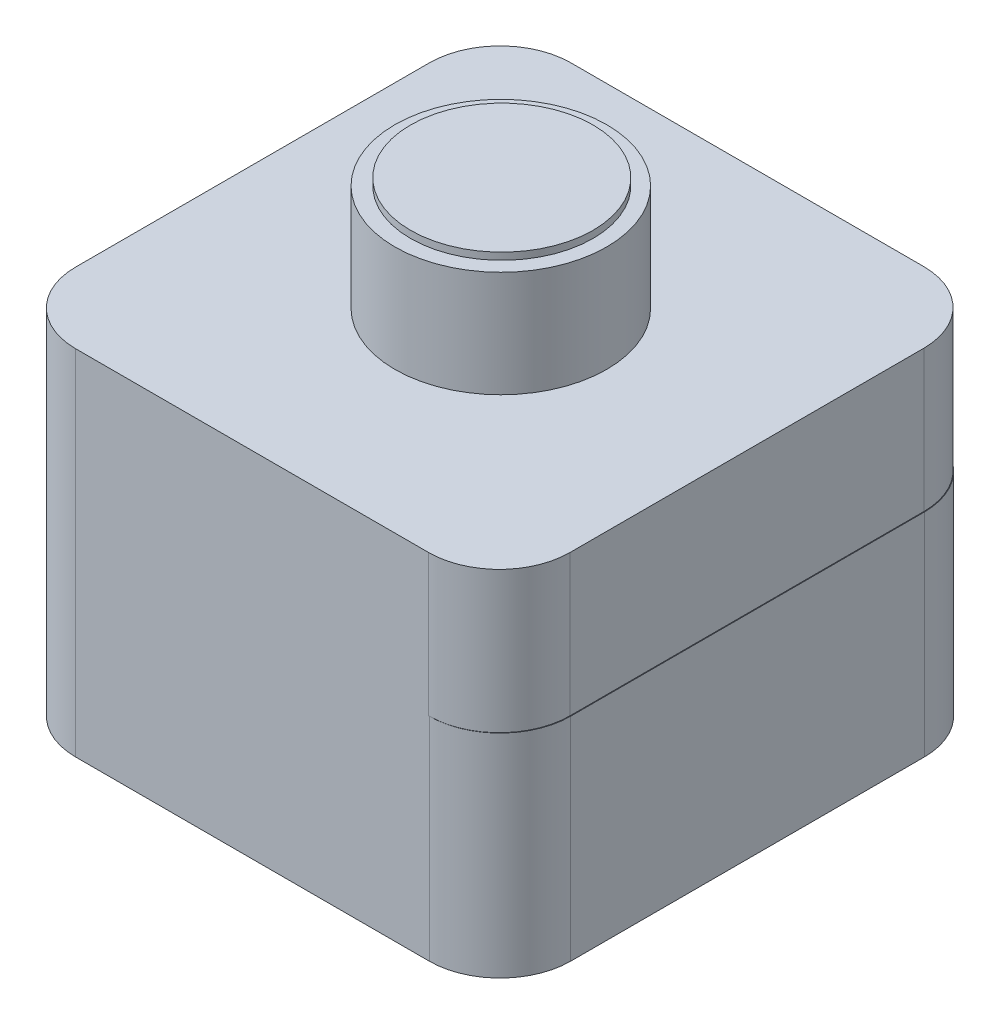
SolidWorks part; units mm, degrees
ref_plane "Alzado" through (0, 0, 0) normal (0, 0, 1) x (1, 0, 0)
ref_plane "Planta" through (0, 0, 0) normal (0, 1, 0) x (1, 0, 0)
ref_plane "Vista lateral" through (0, 0, 0) normal (1, 0, 0) x (0, 0, -1)
sketch "Croquis1" plane through (0, 0, 0) normal (0, 1, 0) x (1, 0, 0)
  line L1 (10, 0) -> (60, 0)
  line L2 (0, 10) -> (0, 60)
  line L3 (10, 70) -> (60, 70)
  line L4 (70, 10) -> (70, 60)
  arc A0 (60, 0) -> (70, 10) centre (60, 10) ccw
  arc A1 (10, 0) -> (0, 10) centre (10, 10) cw
  arc A2 (60, 70) -> (70, 60) centre (60, 60) cw
  arc A3 (0, 60) -> (10, 70) centre (10, 60) cw
  point P7 (70, 0)
  point P10 (0, 0)
  point P15 (0, 70)
  dimension "D3" = 10
  dimension "D1" = 70
  dimension "D2" = 70
extrude "Saliente-Extruir1" add sketch "Croquis1" along normal blind 30
sketch "Croquis2" plane through (0, 30, 0) normal (0, 1, 0) x (1, 0, 0)
  line L1 (10, 0) -> (59.9045, 0)
  line L2 (0, 10) -> (0, 60.0227)
  line L3 (10, 70.0227) -> (59.9045, 70.0227)
  line L4 (69.9045, 10) -> (69.9045, 60.0227)
  arc A0 (59.9045, 0) -> (69.9045, 10) centre (59.9045, 10) ccw
  arc A1 (10, 0) -> (0, 10) centre (10, 10) cw
  arc A2 (59.9045, 70.0227) -> (69.9045, 60.0227) centre (59.9045, 60.0227) cw
  arc A3 (0, 60.0227) -> (10, 70.0227) centre (10, 60.0227) cw
  point P9 (0, 0)
  dimension "D1" = 10
extrude "Saliente-Extruir2" add sketch "Croquis2" along normal blind 20
sketch "Croquis3" plane through (0, 50, 0) normal (0, 1, 0) x (1, 0, 0)
  line L0 (0, 70.0168) -> (70.2181, 0)
  line L1 (0, 0) -> (70.2181, 0)
  line L2 (0, 0) -> (0, 70.0168)
  line L3 (0, 70.0168) -> (70.2181, 70.0168)
  line L4 (70.2181, 0) -> (70.2181, 70.0168)
  line L5 (70.2181, 70.0168) -> (0, 0)
  circle A0 centre (35.1091, 35.0084) radius 14.9775
extrude "Saliente-Extruir3" add sketch "Croquis3" along normal blind 15 contours L5 A0 L0 | L0 A0 L5 | L5 A0 L0 | L0 A0 L5
sketch "Croquis4" plane through (0, 65, 0) normal (0, 1, 0) x (1, 0, 0)
  line L0 (70.358, 0) -> (0, 70.1582)
  line L1 (0, 0) -> (70.358, 0)
  line L2 (0, 0) -> (0, 70.1582)
  line L3 (0, 70.1582) -> (70.358, 70.1582)
  line L4 (70.358, 0) -> (70.358, 70.1582)
  line L5 (0, 0) -> (70.358, 70.1582)
  circle A0 centre (35.179, 35.0791) radius 12.9061
extrude "Saliente-Extruir4" add sketch "Croquis4" along normal blind 1 contours L0 A0 L5 | L5 A0 L0 | L0 A0 L5 | L5 A0 L0
ref_plane "Plano1" through (0, 0, -60) normal (0, -1, 0) x (-1, 0, 0)
